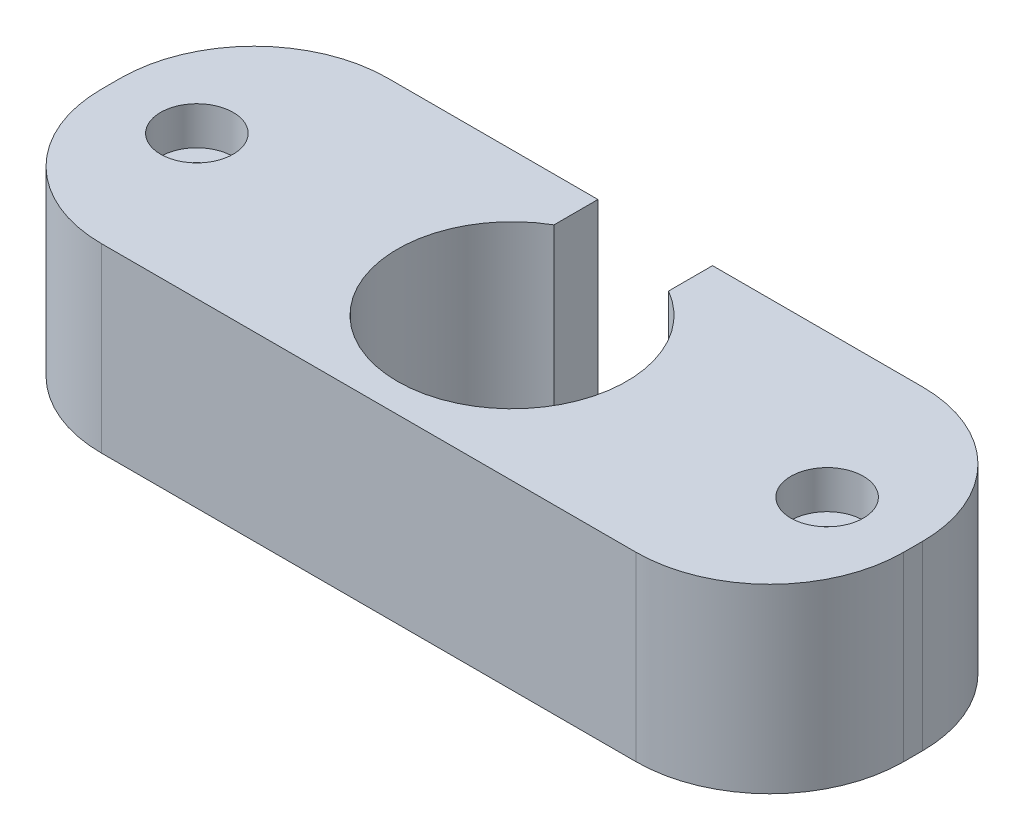
SolidWorks part; units mm, degrees
ref_plane "Front Plane" through (0, 0, 0) normal (0, 0, 1) x (1, 0, 0)
ref_plane "Top Plane" through (0, 0, 0) normal (0, 1, 0) x (1, 0, 0)
ref_plane "Right Plane" through (0, 0, 0) normal (1, 0, 0) x (0, 0, -1)
sketch "Sketch1" plane through (0, 0, 0) normal (0, 1, 0) x (1, 0, 0)
  line L1 (0, 0) -> (42, 0)
  line L2 (0, 0) -> (0, 15)
  line L3 (0, 15) -> (42, 15)
  line L4 (42, 0) -> (42, 15)
  dimension "D1" = 42
  dimension "D2" = 15
extrude "Boss-Extrude1" add sketch "Sketch1" against normal blind 9.5
sketch "Sketch2" plane through (0, 0, 0) normal (0, 1, 0) x (1, 0, 0)
  line L2 (0, 15) -> (0, 0) construction
  line L3 (42, 15) -> (0, 15) construction
  circle A0 centre (21, 7.5) radius 6
  point P4 (0, 7.5)
  point P7 (21, 15)
  dimension "D2" = 12
extrude "Cut-Extrude1" cut sketch "Sketch2" against normal up to next
sketch "Sketch4" plane through (0, 0, 0) normal (0, 1, 0) x (1, 0, 0)
  line L0 (21, 15) -> (21, 0) construction
  line L1 (4.5, 7.5) -> (37.5, 7.5) construction
  line L2 (42, 15) -> (0, 15) construction
  line L3 (0, 0) -> (42, 0) construction
  circle A0 centre (4.5, 7.5) radius 1.9
  circle A1 centre (37.5, 7.5) radius 1.9
  point P6 (21, 7.5)
  point P11 (21, 7.5)
  dimension "D3" = 3.8
  dimension "D1" = 33
extrude "Cut-Extrude3" cut sketch "Sketch4" against normal blind 2
sketch "Sketch5" plane through (0, -9.5, 0) normal (0, -1, 0) x (-1, 0, 0)
  line L3 (-37.5, 7.5) -> (-4.5, 7.5) construction
  line L4 (-21, 15) -> (-21, 0) construction
  line L5 (-42, 15) -> (0, 15) construction
  line L6 (0, 0) -> (-42, 0) construction
  circle A0 centre (-37.5, 7.5) radius 2.05
  circle A1 centre (-4.5, 7.5) radius 2.05
  point P4 (-21, 7.5)
  point P5 (-21, 7.5)
  dimension "D5" = 4.1
  dimension "D6" = 33
extrude "Cut-Extrude4" cut sketch "Sketch5" against normal blind 5
sketch "Sketch6" plane through (0, -2, 0) normal (0, 1, 0) x (1, 0, 0)
  circle A1 centre (4.5, 7.5) radius 0.95
  circle A2 centre (37.5, 7.5) radius 0.95
  circle A3 centre (4.5, 7.5) radius 1.9 construction
  circle A4 centre (37.5, 7.5) radius 1.9 construction
  dimension "D1" = 1.9
extrude "Cut-Extrude5" cut sketch "Sketch6" against normal blind 3
fillet "Fillet1" radius 7 4 edges at (42, -4.75, -15) (0, -4.75, -15) (42, -4.75, 0) (0, -4.75, 0)
sketch "Sketch7" plane through (0, 0, -15) normal (0, 0, -1) x (-1, 0, 0)
  line L0 (-35, 0) -> (-7, 0) construction
  line L1 (-35, -9.5) -> (-7, -9.5) construction
  line L2 (-24, 0) -> (-18, 0)
  line L3 (-24, 0) -> (-24, -9.5)
  line L4 (-24, -9.5) -> (-18, -9.5)
  line L5 (-18, 0) -> (-18, -9.5)
  line L6 (-7, -4.75) -> (-18, -4.75) construction
  line L7 (-7, -9.5) -> (-7, 0) construction
  line L8 (-24, -4.75) -> (-35, -4.75) construction
  line L9 (-35, 0) -> (-35, -9.5) construction
  dimension "D1" = 11
extrude "Cut-Extrude6" cut sketch "Sketch7" against normal blind 3
